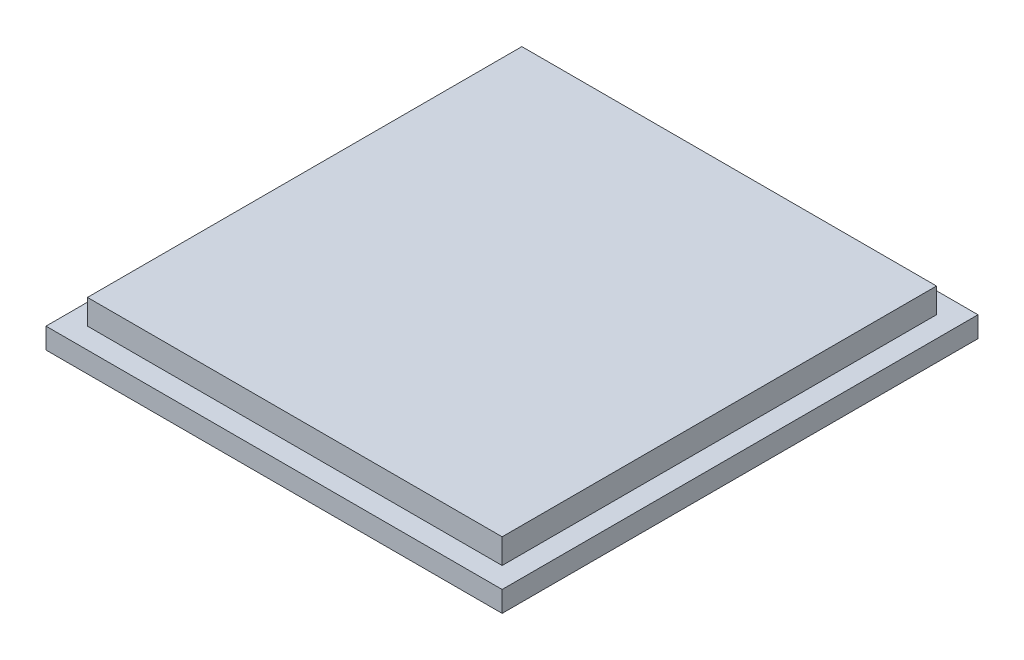
SolidWorks part; units mm, degrees
ref_plane "Front Plane" through (0, 0, 0) normal (0, 0, 1) x (1, 0, 0)
ref_plane "Top Plane" through (0, 0, 0) normal (0, 1, 0) x (1, 0, 0)
ref_plane "Right Plane" through (0, 0, 0) normal (1, 0, 0) x (0, 0, -1)
sketch "Sketch1" plane through (0, 0, 0) normal (0, 1, 0) x (1, 0, 0)
  line L1 (-34.925, -36.4363) -> (34.925, -36.4363)
  line L2 (-34.925, -36.4363) -> (-34.925, 36.4363)
  line L3 (-34.925, 36.4363) -> (34.925, 36.4363)
  line L4 (34.925, -36.4363) -> (34.925, 36.4363)
  line L5 (-34.925, -36.4363) -> (34.925, 36.4363) construction
  line L6 (-34.925, 36.4363) -> (34.925, -36.4363) construction
  point P0 (0, 0)
  dimension "D1" = 72.8726
  dimension "D2" = 69.85
extrude "Boss-Extrude1" add sketch "Sketch1" along normal blind 3.175
sketch "Sketch2" plane through (0, 3.175, 0) normal (0, 1, 0) x (1, 0, 0)
  line L8 (31.75, -33.2613) -> (31.75, 33.2613)
  line L9 (-31.75, -33.2613) -> (31.75, -33.2613)
  line L10 (-31.75, 33.2613) -> (-31.75, -33.2613)
  line L11 (31.75, 33.2613) -> (-31.75, 33.2613)
  line L12 (31.75, -33.2613) -> (31.75, 33.2613)
  line L13 (-31.75, -33.2613) -> (31.75, -33.2613)
  line L14 (-31.75, 33.2613) -> (-31.75, -33.2613)
  line L15 (31.75, 33.2613) -> (-31.75, 33.2613)
  dimension "D1" = 3.175
extrude "Boss-Extrude2" add sketch "Sketch2" along normal blind 3.81
